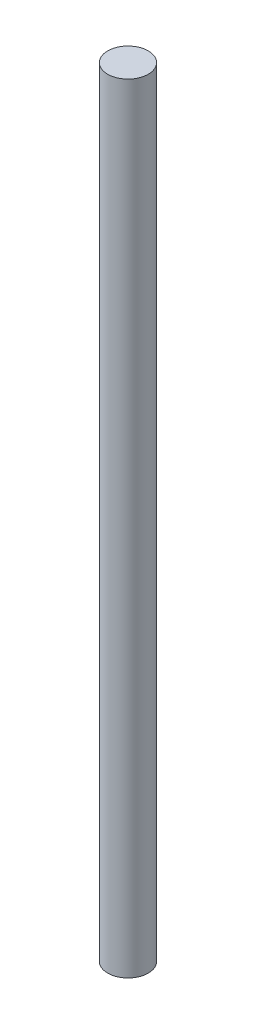
SolidWorks part; units mm, degrees
ref_plane "Front Plane" through (0, 0, 0) normal (0, 0, 1) x (1, 0, 0)
ref_plane "Top Plane" through (0, 0, 0) normal (0, 1, 0) x (1, 0, 0)
ref_plane "Right Plane" through (0, 0, 0) normal (1, 0, 0) x (0, 0, -1)
sketch "Sketch1" plane through (0, 0, 0) normal (0, 1, 0) x (1, 0, 0)
  circle A0 centre (0, 0) radius 15.875
  dimension "D1" = 31.75
extrude "Boss-Extrude1" add sketch "Sketch1" along normal blind 609.6
